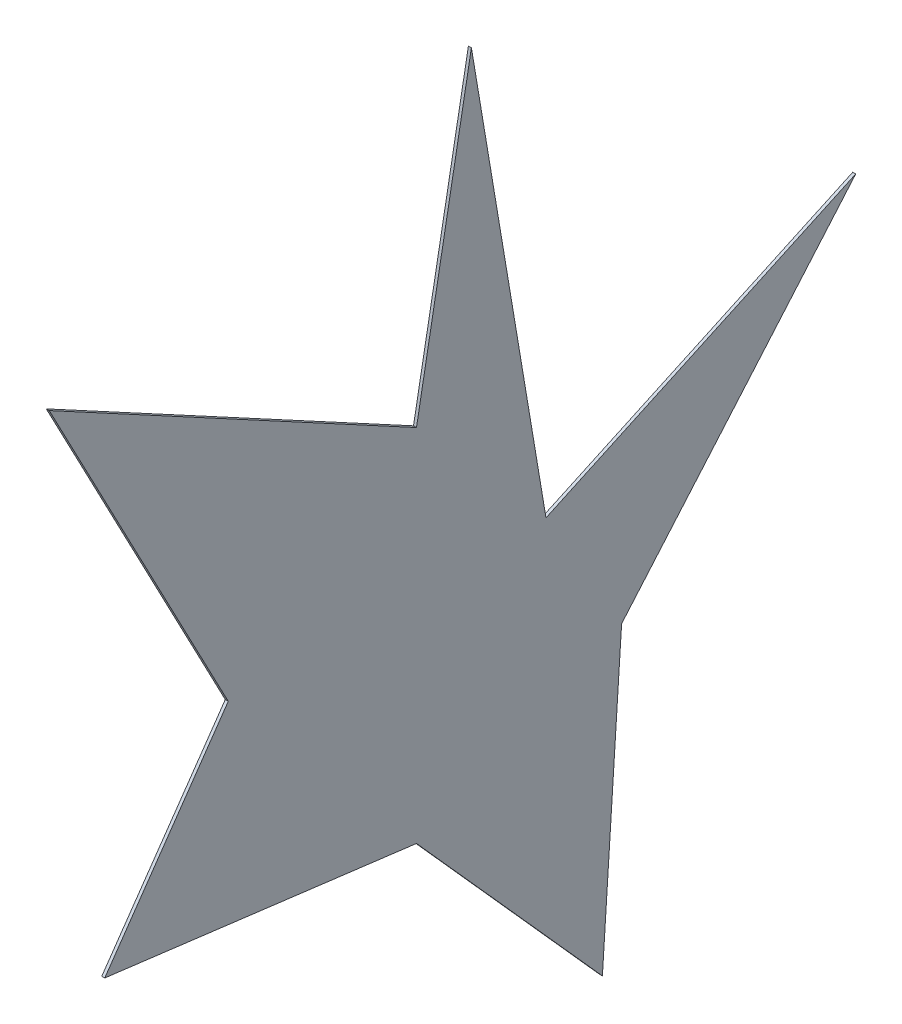
SolidWorks part; units mm, degrees
ref_plane "Front Plane" through (0, 0, 0) normal (0, 0, 1) x (1, 0, 0)
ref_plane "Top Plane" through (0, 0, 0) normal (0, 1, 0) x (1, 0, 0)
ref_plane "Right Plane" through (0, 0, 0) normal (1, 0, 0) x (0, 0, -1)
other "Center of Mass"
sketch "Sketch1" plane through (0, 0, 0) normal (1, 0, 0) x (0, 0, -1)
  line L0 (0, 0) -> (-27.6595, -23.2091)
  line L1 (0, 0) -> (34.9881, -12.7346)
  line L2 (0, 0) -> (71.6245, 0)
  line L3 (0, 0) -> (-54.2532, 19.7465) construction
  line L4 (0, 0) -> (38.3022, 32.1394) construction
  line L5 (0, 0) -> (-10.9729, 62.2306) construction
  line L6 (38.3022, 32.1394) -> (-8.6824, 49.2404)
  line L7 (34.9881, -12.7346) -> (59.2805, -21.5763) construction
  line L8 (-27.6595, -23.2091) -> (34.9881, -12.7346)
  line L9 (59.2805, -21.5763) -> (84.778, -17.3133)
  line L10 (-27.6595, -23.2091) -> (-47.0514, -39.4808) construction
  line L11 (-10.0256, 56.8579) -> (-200.2503, -102.7596)
  line L12 (-200.2503, -102.7596) -> (230.6009, -30.723)
  line L13 (-10.0256, 56.8579) -> (230.6009, -30.723)
  line L14 (34.9881, -12.7346) -> (130.4272, -47.4716)
  line L15 (34.9881, -12.7346) -> (135.1618, 4.014)
  line L16 (104.1175, -413.951) -> (234.7207, -405.4677)
  line L17 (234.7207, -405.4677) -> (321.4195, -470.7235)
  line L18 (321.4195, -470.7235) -> (230.7138, -539.8947)
  line L19 (230.7138, -539.8947) -> (83.8882, -511.8347)
  line L20 (83.8882, -511.8347) -> (104.1175, -413.951)
  line L21 (243.27, -593.1992) -> (24.6509, -551.4187)
  line L22 (24.6509, -551.4187) -> (62.8622, -366.5253)
  line L23 (62.8622, -366.5253) -> (249.9782, -354.3713)
  line L24 (249.9782, -354.3713) -> (404.217, -470.4627)
  line L25 (404.217, -470.4627) -> (243.27, -593.1992)
  line L26 (34.9881, -12.7346) -> (52.0891, 34.25)
  line L27 (34.9881, -12.7346) -> (230.6009, -30.723)
  line L28 (-200.2503, -102.7596) -> (-27.6595, -23.2091)
  line L29 (-740.559, -337.6135) -> (-527.6692, -254.4851)
  line L30 (-527.6692, -254.4851) -> (-430.3481, -444.0584)
  line L31 (-430.3481, -444.0584) -> (-569.2162, -462.2511)
  line L32 (-569.2162, -462.2511) -> (-577.3435, -576.8611)
  line L33 (-577.3435, -576.8611) -> (-740.559, -337.6135)
  line L34 (-529.6954, -753.1726) -> (-832.6119, -309.146)
  line L35 (-832.6119, -309.146) -> (-499.0322, -178.8911)
  line L36 (-499.0322, -178.8911) -> (-338.046, -492.4788)
  line L37 (-338.046, -492.4788) -> (-512.8328, -515.3772)
  line L38 (-512.8328, -515.3772) -> (-529.6954, -753.1726)
  line L39 (-1329.0232, -733.4218) -> (-1116.1334, -650.2934)
  line L40 (-1116.1334, -650.2934) -> (-1018.8123, -839.8668)
  line L41 (-1018.8123, -839.8668) -> (-1065.8976, -937.8389)
  line L42 (-1065.8976, -937.8389) -> (-1165.8077, -972.6695)
  line L43 (-1165.8077, -972.6695) -> (-1329.0232, -733.4218)
  line L49 (-1421.0761, -704.9544) -> (-1087.4964, -574.6994)
  line L50 (-1087.4964, -574.6994) -> (-951.8197, -838.9864)
  line L51 (-951.8197, -838.9864) -> (-1022.614, -986.2909)
  line L52 (-1022.614, -986.2909) -> (-1189.4652, -1044.4585)
  line L53 (-1189.4652, -1044.4585) -> (-1421.0761, -704.9544)
  line L54 (-294.6871, -1271.026) -> (-1018.8123, -1271.026)
  line L55 (-529.6954, -753.1726) -> (-607.734, -420.5955)
  line L56 (-607.734, -420.5955) -> (-338.046, -492.4788)
  line L57 (-1018.8123, -1271.026) -> (-577.3435, -1457.704)
  line L58 (-577.3435, -1457.704) -> (-529.6954, -1894.4945)
  line L59 (-529.6954, -1894.4945) -> (-265.6886, -1537.45)
  line L60 (-249.834, -1221.026) -> (-213.8678, -1551.4655)
  line L61 (-565.5312, -2027.0572) -> (-213.8678, -1551.4655)
  line L62 (-529.6954, -753.1726) -> (-338.046, -492.4788)
  line L63 (-1189.4652, -1044.4585) -> (-1116.1334, -882.6321)
  line L64 (-1116.1334, -882.6321) -> (-951.8197, -838.9864)
  line L65 (-623.8641, -1492.319) -> (-565.5312, -2027.0572)
  line L66 (-1265.4359, -1221.026) -> (-623.8641, -1492.319)
  line L67 (-249.834, -1221.026) -> (-1265.4359, -1221.026)
  line L68 (-339.5402, -1321.026) -> (-317.5094, -1523.4346)
  line L69 (-493.8596, -1761.9318) -> (-317.5094, -1523.4346)
  line L70 (-530.8229, -1423.0891) -> (-493.8596, -1761.9318)
  line L71 (-294.6871, -1271.026) -> (-265.6886, -1537.45)
  line L72 (-772.1887, -1321.026) -> (-530.8229, -1423.0891)
  line L73 (-339.5402, -1321.026) -> (-772.1887, -1321.026)
  line L82 (-2162.4163, -2137.7103) -> (-1914.4952, -1614.0434)
  line L83 (-1914.4952, -1614.0434) -> (-1233.4749, -1614.0434)
  line L84 (-1233.4749, -1614.0434) -> (-1165.8077, -2365.1126)
  line L88 (-1165.8077, -2365.1126) -> (-1818.9149, -2635.1719)
  line L89 (-1818.9149, -2635.1719) -> (-2162.4163, -2137.7103)
  line L90 (-3954.9183, -2387.628) -> (-3770.3384, -1374.1798)
  line L91 (-3770.3384, -1374.1798) -> (-3519.5884, -2868.2322)
  line L92 (-3519.5884, -2868.2322) -> (-2478.2791, -2387.628)
  line L93 (-2478.2791, -2387.628) -> (-3265.3557, -3303.5622)
  line L94 (-3265.3557, -3303.5622) -> (-3329.9377, -4296.6996)
  line L95 (-3329.9377, -4296.6996) -> (-3954.9183, -3598.6114)
  line L96 (-3954.9183, -3598.6114) -> (-5002.9421, -3466.2154)
  line L97 (-5002.9421, -3466.2154) -> (-4587.7, -2868.2322)
  line L98 (-4587.7, -2868.2322) -> (-5189.5001, -1720.995)
  line L99 (-5189.5001, -1720.995) -> (-3954.9183, -2387.628)
  line L100 (-6496.0704, -3303.5622) -> (-6630.8007, -4808.2711)
  line L101 (-6630.8007, -4808.2711) -> (-5407.0007, -5229.3032)
  line L102 (-6446.2696, -3308.0213) -> (-6577.5078, -4773.7295)
  line L103 (-6577.5078, -4773.7295) -> (-5390.7346, -5182.023)
  point P28 (85.2093, -17.3529)
  point P29 (-66.1981, -40.9723)
  point P69 (-551.1108, -1442.7474)
  point P81 (-2873, -4958)
  point P83 (-5407.0007, -5229.3032)
  dimension "D9" = 50
  dimension "D1" = 50
  dimension "D2" = 50
  dimension "D3" = 100
  dimension "D4" = 50
  dimension "D5" = 50
  dimension "D6" = 50
  dimension "D7" = 43.3013
  dimension "D8" = 43.3013
  dimension "D10" = 101.5642
  dimension "D11" = 101.5642
  dimension "D12" = 94.9686
  dimension "D13" = 90
  dimension "D14" = 29.492
  dimension "D15" = 196.4382
  dimension "D16" = 57.735
  dimension "D17" = 60
  dimension "D19" = 50
  dimension "D21" = 50
  dimension "D18" = 60
  dimension "D20" = 50
extrude "Boss-Extrude1" add sketch "Sketch1" along normal blind 10 contours L99 L90 L91 L92 L93 L94 L95 L96 L97 L98
